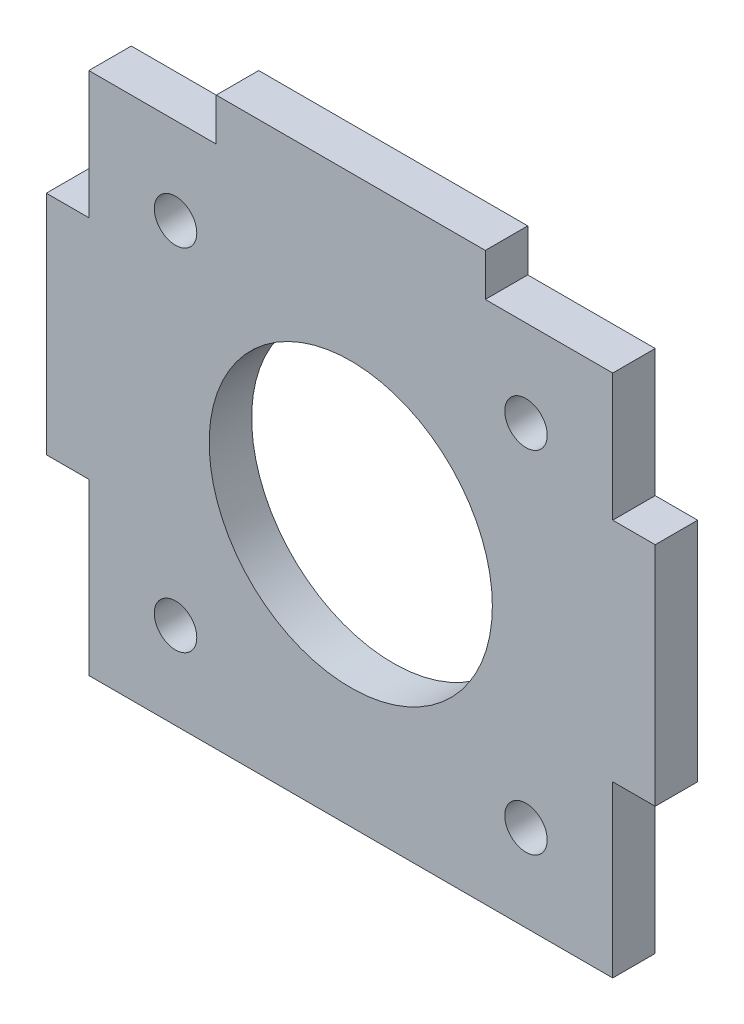
SolidWorks part; units mm, degrees
ref_plane "Front Plane" through (0, 0, 0) normal (0, 0, 1) x (1, 0, 0)
ref_plane "Top Plane" through (0, 0, 0) normal (0, 1, 0) x (1, 0, 0)
ref_plane "Right Plane" through (0, 0, 0) normal (1, 0, 0) x (0, 0, -1)
sketch "Sketch1" plane through (0, 0, 0) normal (0, 0, 1) x (1, 0, 0)
  line L0 (-12.3744, 12.3744) -> (12.3744, -12.3744) construction
  line L1 (-21.5, 21.5) -> (21.5, 21.5)
  line L2 (-21.5, 21.5) -> (-21.5, -21.5)
  line L3 (-21.5, -21.5) -> (21.5, -21.5)
  line L4 (21.5, 21.5) -> (21.5, -21.5)
  line L5 (-21.5, 21.5) -> (21.5, -21.5) construction
  line L6 (-21.5, -21.5) -> (21.5, 21.5) construction
  line L7 (12.3744, 12.3744) -> (-12.3744, -12.3744) construction
  circle A0 centre (-12.3744, 12.3744) radius 1.5
  circle A1 centre (12.3744, -12.3744) radius 1.5
  circle A2 centre (12.3744, 12.3744) radius 1.5
  circle A3 centre (-12.3744, -12.3744) radius 1.5
  circle A4 centre (0, 0) radius 10
  point P0 (0, 0)
  point P9 (0, 0)
  point P12 (0, 0)
  dimension "D1" = 3
  dimension "D6" = 20
  dimension "D2" = 17.5
  dimension "D3" = 45
  dimension "D4" = 43
  dimension "D5" = 43
extrude "Boss-Extrude1" add sketch "Sketch1" along normal blind 3
sketch "Sketch2" plane through (0, 0, 3) normal (0, 0, 1) x (1, 0, 0)
  line L0 (21.5, -21.5) -> (21.5, 21.5) construction
  line L1 (-21.5, -21.5) -> (21.5, -21.5)
  line L2 (-21.5, -21.5) -> (-21.5, -18.5)
  line L3 (-18.5, -18.5) -> (18.5, -18.5)
  line L4 (21.5, -21.5) -> (21.5, -18.5)
  line L5 (-21.5, 9.5) -> (-18.5, 9.5)
  line L6 (-21.5, 21.5) -> (-21.5, -21.5) construction
  line L7 (-18.5, 9.5) -> (-18.5, 18.5)
  line L8 (-18.5, 18.5) -> (-9.5, 18.5)
  line L9 (-9.5, 18.5) -> (-9.5, 21.5)
  line L10 (21.5, 21.5) -> (-21.5, 21.5) construction
  line L11 (-21.5, 9.5) -> (-21.5, 21.5)
  line L12 (-21.5, 21.5) -> (-9.5, 21.5)
  line L13 (0, 0) -> (0, -3.5321) construction
  line L14 (21.5, 9.5) -> (21.5, 21.5)
  line L15 (21.5, 9.5) -> (18.5, 9.5)
  line L16 (18.5, 9.5) -> (18.5, 18.5)
  line L17 (18.5, 18.5) -> (9.5, 18.5)
  line L18 (9.5, 18.5) -> (9.5, 21.5)
  line L19 (21.5, 21.5) -> (9.5, 21.5)
  line L20 (-21.5, -18.5) -> (-18.5, -18.5) construction
  line L21 (-21.5, -18.5) -> (-18.5, -18.5) construction
  line L22 (-21.5, -18.5) -> (-21.5, -6.5)
  line L23 (-21.5, -6.5) -> (-18.5, -6.5)
  line L24 (-18.5, -18.5) -> (-18.5, -6.5)
  line L25 (21.5, -18.5) -> (18.5, -18.5) construction
  line L26 (21.5, -18.5) -> (21.5, -6.5)
  line L27 (21.5, -6.5) -> (18.5, -6.5)
  line L28 (18.5, -18.5) -> (18.5, -6.5)
  line L29 (18.5, -18.5) -> (21.5, -18.5) construction
  dimension "D1" = 3
  dimension "D2" = 3
  dimension "D3" = 3
  dimension "D4" = 12
  dimension "D5" = 12
  dimension "D6" = 3
  dimension "D7" = 12
extrude "Cut-Extrude1" cut sketch "Sketch2" against normal blind 3
